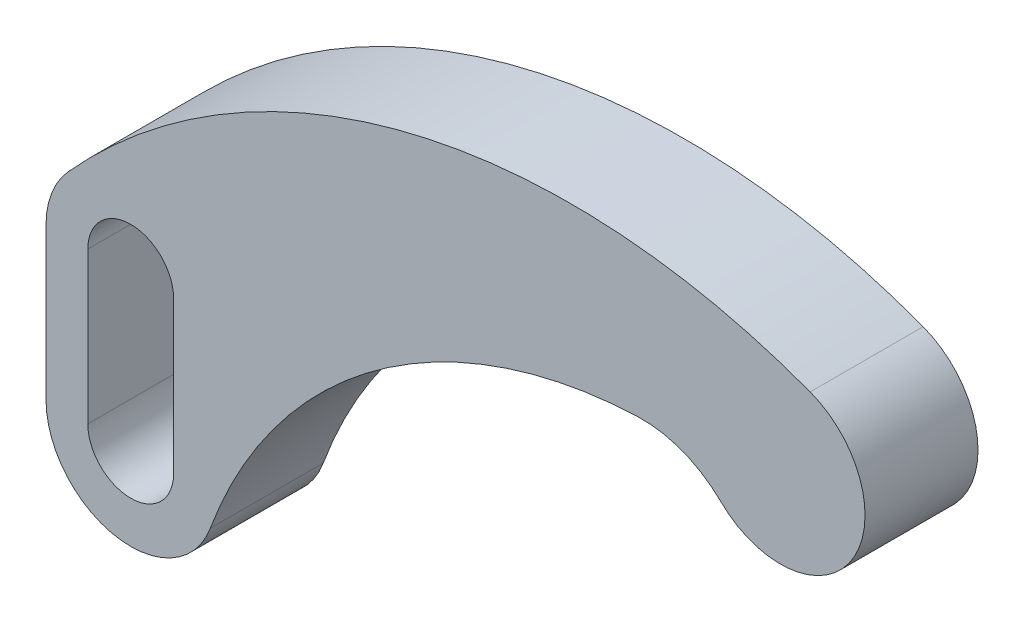
SolidWorks part; units mm, degrees
ref_plane "Front Plane" through (0, 0, 0) normal (0, 0, 1) x (1, 0, 0)
ref_plane "Top Plane" through (0, 0, 0) normal (0, 1, 0) x (1, 0, 0)
ref_plane "Right Plane" through (0, 0, 0) normal (1, 0, 0) x (0, 0, -1)
sketch "Sketch1" plane through (0, 0, 0) normal (0, 0, 1) x (1, 0, 0)
  line L2 (-165.1, -69.596) -> (-165.1, -35.56)
  line L3 (-155.702, -35.56) -> (-155.702, -69.596)
  line L4 (-136.398, -35.56) -> (-136.398, -69.596)
  arc A0 (-13.3322, -13.6071) -> (6.7095, 17.8293) centre (0, 0) ccw
  arc A1 (-13.3322, -13.6071) -> (-32.0677, -6.3681) centre (-31.1085, -31.75) ccw
  arc A2 (6.7095, 17.8293) -> (-160.2048, -22.8107) centre (-46.9667, -124.8053) ccw
  arc A4 (-165.1, -69.596) -> (-128.1696, -76.1681) centre (-146.05, -69.596) ccw
  arc A5 (-160.2048, -22.8107) -> (-165.1, -35.56) centre (-146.05, -35.56) ccw
  arc A6 (-136.398, -35.56) -> (-155.702, -35.56) centre (-146.05, -35.56) ccw
  arc A7 (-155.702, -69.596) -> (-136.398, -69.596) centre (-146.05, -69.596) ccw
  arc A8 (-32.0677, -6.3681) -> (-128.1696, -76.1681) centre (-28.0392, -112.972) ccw
  point P3 (0, 0)
  dimension "D1" = 19.05
  dimension "D3" = 25.4
  dimension "D4" = 152.4
  dimension "D5" = 9.652
  dimension "D6" = 19.05
  dimension "D8" = 69.596
  dimension "D9" = 106.68
  dimension "D2" = 31.75
  dimension "D7" = 34.036
  dimension "D10" = 146.05
extrude "Boss-Extrude1" add sketch "Sketch1" along normal blind 25.4
